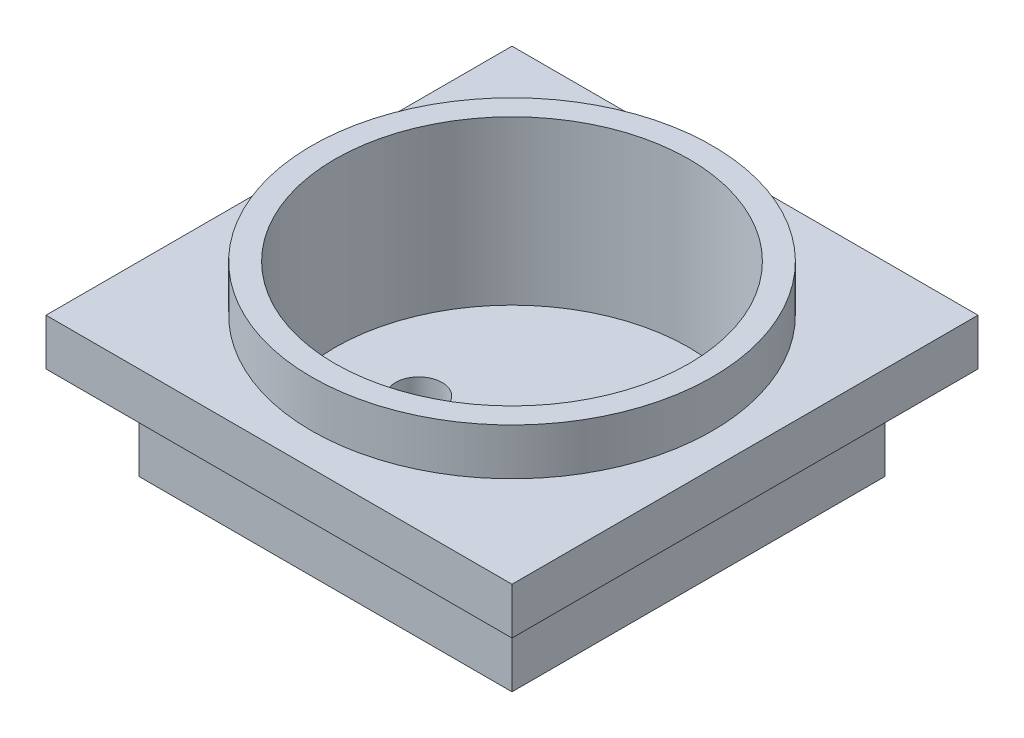
SolidWorks part; units mm, degrees
ref_plane "Alzado" through (0, 0, 0) normal (0, 0, 1) x (1, 0, 0)
ref_plane "Planta" through (0, 0, 0) normal (0, 1, 0) x (1, 0, 0)
ref_plane "Vista lateral" through (0, 0, 0) normal (1, 0, 0) x (0, 0, -1)
sketch "Croquis1" plane through (0, 0, 0) normal (0, 1, 0) x (1, 0, 0)
  line L1 (-25, 25) -> (25, 25)
  line L2 (-25, 25) -> (-25, -25)
  line L3 (-25, -25) -> (25, -25)
  line L4 (25, 25) -> (25, -25)
  line L5 (-25, 25) -> (25, -25) construction
  line L6 (-25, -25) -> (25, 25) construction
  point P0 (0, 0)
  dimension "D1" = 50
extrude "Saliente-Extruir1" add sketch "Croquis1" along normal blind 5
sketch "Croquis2" plane through (0, 5, 0) normal (0, 1, 0) x (1, 0, 0)
  circle A0 centre (0, 0) radius 21.5
  dimension "D1" = 43
extrude "Saliente-Extruir2" add sketch "Croquis2" along normal blind 5
sketch "Croquis4" plane through (0, 0, 0) normal (0, -1, 0) x (1, 0, 0)
  line L1 (20, -20) -> (-20, -20)
  line L2 (20, -20) -> (20, 20)
  line L3 (20, 20) -> (-20, 20)
  line L4 (-20, -20) -> (-20, 20)
  line L5 (20, -20) -> (-20, 20) construction
  line L6 (20, 20) -> (-20, -20) construction
  point P0 (0, 0)
  dimension "D1" = 40
extrude "Saliente-Extruir3" add sketch "Croquis4" along normal blind 10
sketch "Croquis3" plane through (0, 10, 0) normal (0, 1, 0) x (1, 0, 0)
  circle A0 centre (0, 0) radius 19
  dimension "D1" = 38
extrude "Cortar-Extruir1" cut sketch "Croquis3" against normal blind 17.5
sketch "Croquis5" plane through (0, -7.5, 0) normal (0, 1, 0) x (1, 0, 0)
  line L0 (0, 0) -> (0, 50000) construction
  circle A0 centre (10, 0) radius 2.5
  circle A1 centre (-10, 0) radius 2.5
  dimension "D2" = 5
  dimension "D1" = 10
extrude "Cortar-Extruir2" cut sketch "Croquis5" against normal through all
